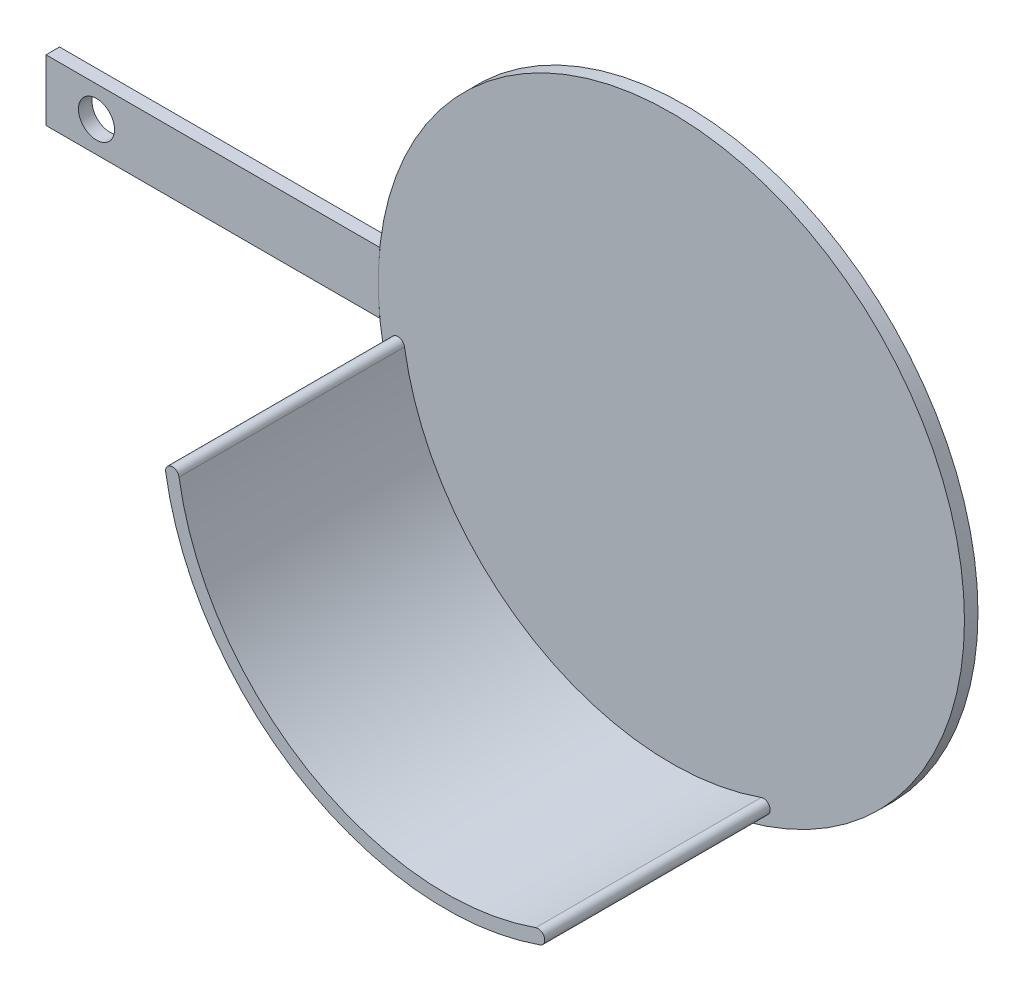
SolidWorks part; units mm, degrees
ref_plane "Plan de face" through (0, 0, 0) normal (0, 0, 1) x (1, 0, 0)
ref_plane "Plan de dessus" through (0, 0, 0) normal (0, 1, 0) x (1, 0, 0)
ref_plane "Plan de droite" through (0, 0, 0) normal (1, 0, 0) x (0, 0, -1)
sketch "Esquisse1" plane through (0, 0, 0) normal (0, 0, 1) x (1, 0, 0)
  circle A0 centre (0, 0) radius 65
  dimension "D1" = 130
extrude "Boss.-Extru.1" add sketch "Esquisse1" along normal blind 3
sketch "Esquisse2" plane through (0, 0, 3) normal (0, 0, 1) x (1, 0, 0)
  line L2 (0, 0) -> (-47.3168, -44.5659) construction
  line L4 (-61.9722, 1.8555) -> (-64.9709, 1.9452)
  line L5 (-1.8555, -61.9722) -> (-1.9452, -64.9709)
  arc A3 (-1.9452, -64.9709) -> (-64.9709, 1.9452) centre (0, 0) cw
  arc A4 (-1.8555, -61.9722) -> (-61.9722, 1.8555) centre (0, 0) cw
extrude "Boss.-Extru.2" [suppressed] add sketch "Esquisse2" along normal blind 60
sketch "Esquisse3" plane through (0, 0, 0) normal (0, 0, -1) x (-1, 0, 0)
  line L0 (0, 0) -> (113.8804, 0) construction
  line L1 (0, 0) -> (64.6439, 6.7944) construction
  line L2 (0, 0) -> (64.6439, -6.7944) construction
  line L3 (64.6439, 6.7944) -> (138.6725, 6.7944)
  line L4 (64.6439, -6.7944) -> (138.6725, -6.7944)
  line L5 (138.6725, -6.7944) -> (138.6725, 6.7944)
  arc A0 (64.6439, -6.7944) -> (64.6439, 6.7944) centre (0, 0) ccw
  circle A1 centre (0, 0) radius 65 construction
  dimension "D1" = 6
  dimension "D2" = 6
extrude "Boss.-Extru.3" add sketch "Esquisse3" against normal blind 3 separate body
sketch "Esquisse4" plane through (0, 0, 3) normal (0, 0, 1) x (1, 0, 0)
  circle A0 centre (-127.4771, 0) radius 4
extrude "Enlèv. mat.-Extru.1" cut sketch "Esquisse4" against normal blind 3
sketch "Esquisse5" plane through (0, 0, 3) normal (0, 0, 1) x (1, 0, 0)
  line L0 (39.6348, 66.7422) -> (-113.5458, -191.2029) construction
  arc A0 (-59.1775, -9.5609) -> (19.9257, -56.5363) centre (0, 0) ccw
  arc A1 (-62.1391, -10.0394) -> (20.9229, -59.3657) centre (0, 0) ccw
  arc A2 (-59.1775, -9.5609) -> (-62.1391, -10.0394) centre (-60.6583, -9.8001) ccw
  arc A3 (19.9257, -56.5363) -> (20.9229, -59.3657) centre (20.4243, -57.951) cw
  dimension "D1" = 46
  dimension "D2" = 46
  dimension "D3" = 3
extrude "Boss.-Extru.4" add sketch "Esquisse5" along normal blind 50
